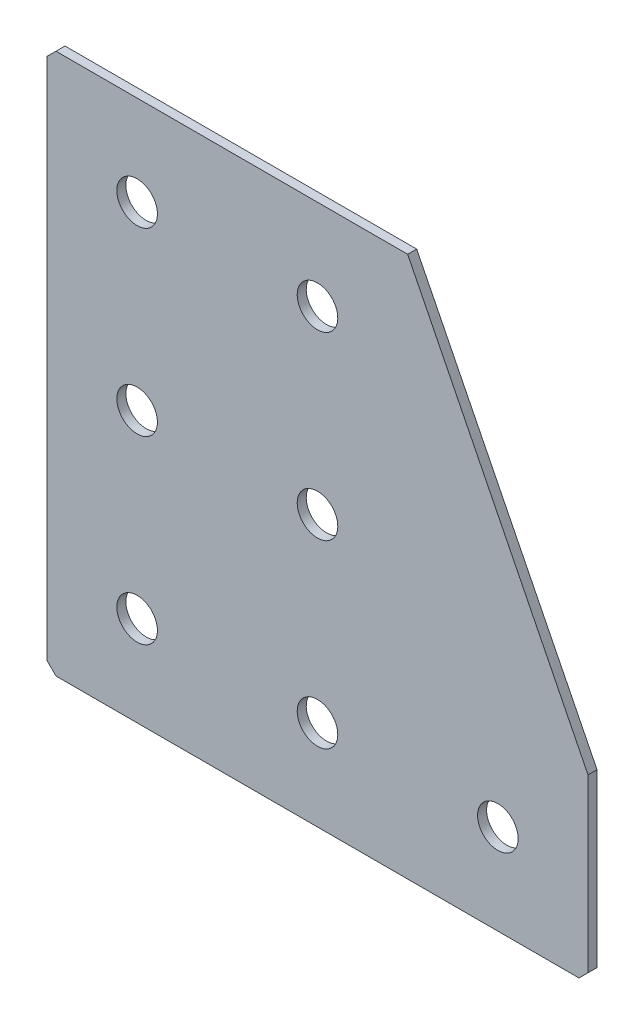
SolidWorks part; units mm, degrees
material "Простая углеродистая сталь"
ref_plane "Спереди(Плоскость XY)" through (0, 0, 0) normal (0, 0, 1) x (1, 0, 0)
ref_plane "Сверху(Плоскость XZ)" through (0, 0, 0) normal (0, 1, 0) x (1, 0, 0)
ref_plane "Справа(Плоскость ZY)" through (0, 0, 0) normal (1, 0, 0) x (0, 0, -1)
sketch "Эскиз1" plane through (0, 0, 0) normal (0, 0, -1) x (1, 0, 0)
  line L0 (0, 0) -> (0, 120)
  line L1 (0, 120) -> (120, 120)
  line L2 (120, 120) -> (120, 80)
  line L3 (120, 80) -> (80, 80) construction
  line L4 (80, 80) -> (80, 0) construction
  line L5 (80, 0) -> (0, 0)
  line L6 (120, 80) -> (80, 0)
  dimension "D1" = 120
  dimension "D2" = 40
  dimension "D3" = 80
extrude "Бобышка-Вытянуть1" add sketch "Эскиз1" along normal blind 2
hole_wizard "Отверстие с зазором M81" positions "Эскиз2" profile "Эскиз3" hole size "M8" standard "IS" end condition through all
sketch "Эскиз2" plane through (0, 0, -2) normal (0, 0, -1) x (1, 0, 0)
  line L0 (20, 0) -> (20, 120) construction
  line L1 (0, 0) -> (80, 0) construction
  line L2 (120, 120) -> (0, 120) construction
  line L3 (120, 100) -> (0, 100) construction
  line L4 (120, 80) -> (120, 120) construction
  line L5 (0, 120) -> (0, 0) construction
  point P0 (60, 100)
  point P2 (20, 100)
  point P4 (20, 60)
  point P6 (20, 20)
  point P21 (100, 100)
  point P24 (60, 60)
  point P26 (60, 20)
  dimension "D1" = 40
  dimension "D2" = 40
  dimension "D3" = 40
  dimension "D4" = 20
  dimension "D5" = 40
  dimension "D6" = 20
sketch "Эскиз3" plane through (60, -100, -2) normal (1, 0, 0) x (0, 1, 0)
  line L0 (0, 0) -> (0, 2)
  line L1 (0, 2) -> (4.5, 2)
  line L2 (4.5, 2) -> (4.5, 0)
  line L5 (4.5, 0) -> (0, 0)
  line L11 (0, -6.35) -> (0, 107.95) construction
  dimension "Диаметр сквозного отверстия" = 9
  dimension "Глубина сквозного отверстия" = 2
chamfer "Фаска1" distance 2 angle 45 3 edges at (0, 0, -1) (120, -120, -1) (0, -120, -1)
